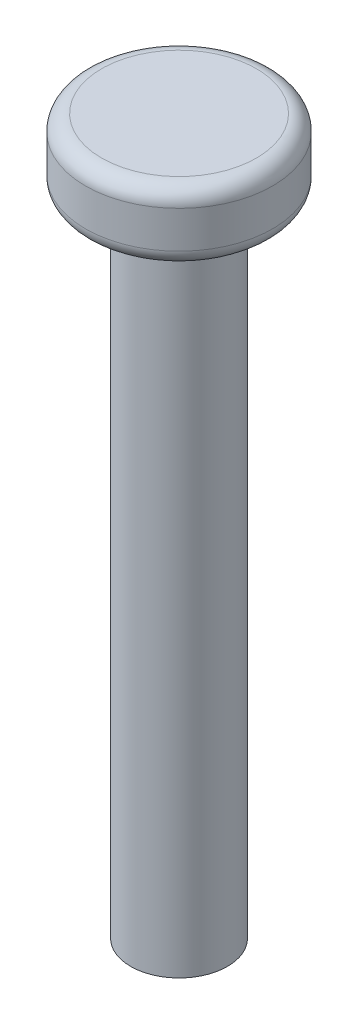
SolidWorks part; units mm, degrees
ref_plane "Спереди" through (0, 0, 0) normal (0, 0, 1) x (1, 0, 0)
ref_plane "Сверху" through (0, 0, 0) normal (0, 1, 0) x (1, 0, 0)
ref_plane "Справа" through (0, 0, 0) normal (1, 0, 0) x (0, 0, -1)
sketch "Sketch1" plane through (0, 0, 0) normal (0, 1, 0) x (1, 0, 0)
  circle A0 centre (0, 0) radius 3
  dimension "D1" = 6
extrude "Boss-Extrude1" add sketch "Sketch1" along normal blind 40
sketch "Sketch2" plane through (0, 40, 0) normal (0, 1, 0) x (1, 0, 0)
  circle A0 centre (0, 0) radius 5.8
  dimension "D1" = 11.6
extrude "Boss-Extrude2" add sketch "Sketch2" along normal blind 4.3
fillet "Fillet1" radius 1 2 edges at (0, 40, 5.8) (0, 44.3, 5.8)
